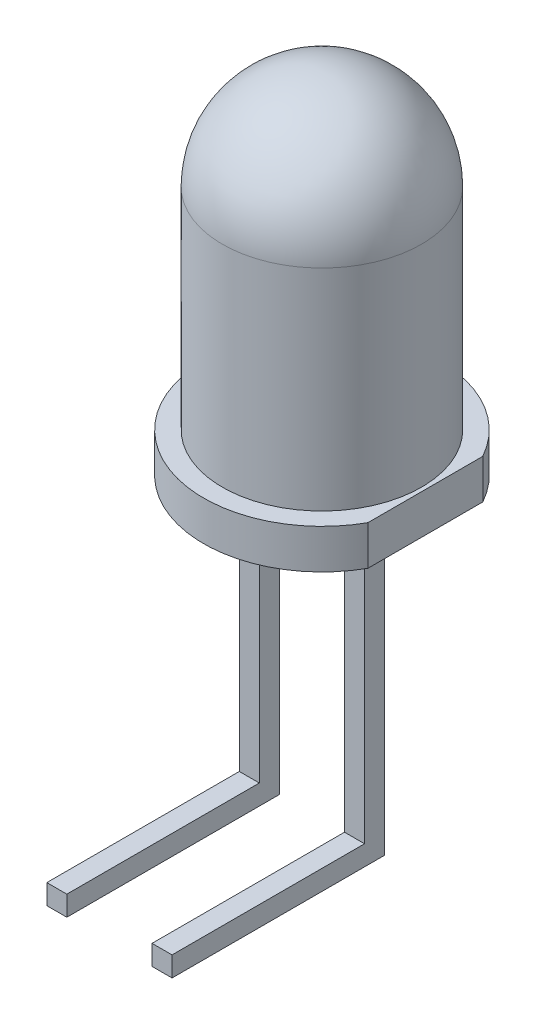
SolidWorks part; units mm, degrees
ref_plane "Front Plane" through (0, 0, 0) normal (0, 0, 1) x (1, 0, 0)
ref_plane "Top Plane" through (0, 0, 0) normal (0, 1, 0) x (1, 0, 0)
ref_plane "Right Plane" through (0, 0, 0) normal (1, 0, 0) x (0, 0, -1)
sketch "Sketch3" plane through (0, 0, 0) normal (0, 0, 1) x (1, 0, 0)
  line L0 (-2.4638, 5.207) -> (-2.4638, 0)
  line L1 (-2.4638, 0) -> (0, 0)
  line L2 (0, 0) -> (0, 7.6708) construction
  line L3 (0, 7.6708) -> (0, 0)
  arc A0 (0, 7.6708) -> (-2.4638, 5.207) centre (0, 5.207) ccw
  dimension "D3" = 2.4638
  dimension "D1" = 7.6708
  dimension "D2" = 2.4638
revolve "Revolve1" add sketch "Sketch3" angle 360 about L2
sketch "Sketch4" plane through (0, 0, 0) normal (0, -1, 0) x (1, 0, 0)
  line L0 (2.5591, 1.4215) -> (2.5591, -1.4215)
  arc A0 (2.5591, 1.4215) -> (2.5591, -1.4215) centre (0, 0) ccw
  dimension "D1" = 5.8547
  dimension "D2" = 2.559
extrude "Boss-Extrude2" add sketch "Sketch4" along normal blind 0.9779
sketch "Sketch5" plane through (0, 0, 0) normal (0, 0, 1) x (1, 0, 0)
  line L0 (-2.9274, -0.9779) -> (2.5591, -0.9779) construction
  line L1 (0, 0) -> (0, -50000) construction
  line L2 (-1.5494, -0.9779) -> (-1.0541, -0.9779)
  line L3 (-1.5494, -0.9779) -> (-1.5494, -8.3439)
  line L4 (-1.5494, -8.3439) -> (-1.0541, -8.3439)
  line L5 (-1.0541, -0.9779) -> (-1.0541, -8.3439)
  line L6 (-1.5494, -0.9779) -> (-1.0541, -8.3439) construction
  line L7 (-1.5494, -8.3439) -> (-1.0541, -0.9779) construction
  line L8 (1.5494, -8.3439) -> (1.0541, -0.9779) construction
  line L9 (1.5494, -0.9779) -> (1.0541, -8.3439) construction
  line L10 (1.0541, -0.9779) -> (1.0541, -8.3439)
  line L11 (1.5494, -8.3439) -> (1.0541, -8.3439)
  line L12 (1.5494, -0.9779) -> (1.5494, -8.3439)
  line L13 (1.5494, -0.9779) -> (1.0541, -0.9779)
  point P0 (-1.3017, -4.6609)
  point P15 (1.3018, -4.6609)
  dimension "D1" = 0.4953
  dimension "D2" = 7.366
  dimension "D3" = 1.5494
extrude "Boss-Extrude3" add sketch "Sketch5" along normal blind 0.4953
sketch "Sketch6" plane through (0, 0, 0.4953) normal (0, 0, 1) x (1, 0, 0)
  line L0 (-1.5494, -0.9779) -> (-1.5494, -8.3439) construction
  line L1 (-1.5494, -7.8486) -> (-1.0541, -7.8486)
  line L2 (-1.5494, -7.8486) -> (-1.5494, -8.3439)
  line L3 (-1.5494, -8.3439) -> (-1.0541, -8.3439)
  line L4 (-1.0541, -7.8486) -> (-1.0541, -8.3439)
  line L5 (-1.5494, -7.8486) -> (-1.0541, -8.3439) construction
  line L6 (-1.5494, -8.3439) -> (-1.0541, -7.8486) construction
  point P0 (-1.3017, -8.0962)
extrude "Boss-Extrude4" add sketch "Sketch6" along normal blind 4.7625
sketch "Sketch7" plane through (0, 0, 0.4953) normal (0, 0, 1) x (1, 0, 0)
  line L0 (1.0541, -0.9779) -> (1.0541, -8.3439) construction
  line L1 (1.0541, -7.8486) -> (1.5494, -7.8486)
  line L2 (1.0541, -7.8486) -> (1.0541, -8.3439)
  line L3 (1.0541, -8.3439) -> (1.5494, -8.3439)
  line L4 (1.5494, -7.8486) -> (1.5494, -8.3439)
  line L5 (1.0541, -7.8486) -> (1.5494, -8.3439) construction
  line L6 (1.0541, -8.3439) -> (1.5494, -7.8486) construction
  point P0 (1.3018, -8.0962)
extrude "Boss-Extrude5" add sketch "Sketch7" along normal blind 4.7625
